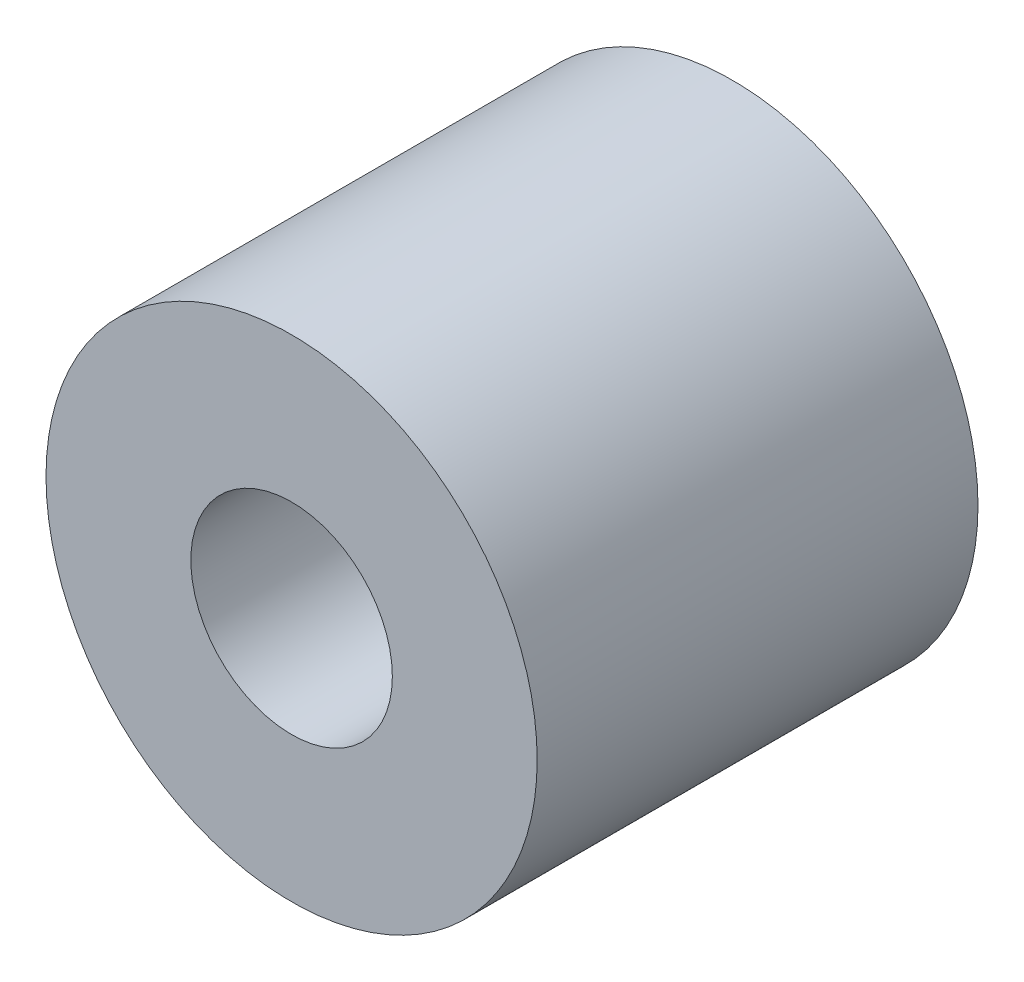
SolidWorks part; units mm, degrees
ref_plane "Front Plane" through (0, 0, 0) normal (0, 0, 1) x (1, 0, 0)
ref_plane "Top Plane" through (0, 0, 0) normal (0, 1, 0) x (1, 0, 0)
ref_plane "Right Plane" through (0, 0, 0) normal (1, 0, 0) x (0, 0, -1)
sketch "Sketch1" plane through (0, 0, 0) normal (0, 0, 1) x (1, 0, 0)
  circle A0 centre (0, 0) radius 3.9
  circle A1 centre (0, 0) radius 1.6
  point P2 (0, 0)
  point P4 (0, 0)
  dimension "D1" = 3.2
  dimension "D2" = 7.8
extrude "Boss-Extrude1" add sketch "Sketch1" along normal blind 7
